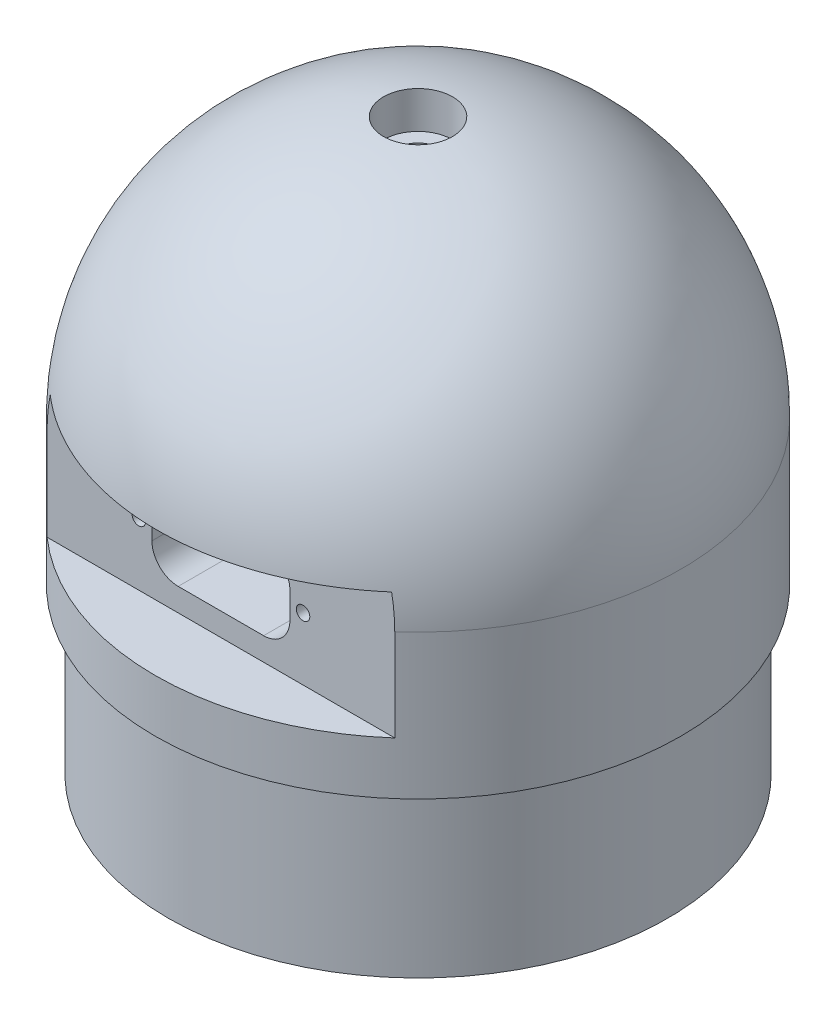
SolidWorks part; units mm, degrees
material "PE haute densité"
ref_plane "Plan de face" through (0, 0, 0) normal (0, 0, 1) x (1, 0, 0)
ref_plane "Plan de dessus" through (0, 0, 0) normal (0, 1, 0) x (1, 0, 0)
ref_plane "Plan de droite" through (0, 0, 0) normal (1, 0, 0) x (0, 0, -1)
sketch "Esquisse1" plane through (0, 0, 0) normal (0, 1, 0) x (1, 0, 0)
  circle A0 centre (0, 0) radius 40
extrude "Boss.-Extru.1" add sketch "Esquisse1" along normal blind 87
fillet "Congé1" radius 40 1 edges at (0, 87, 40)
sketch "Esquisse2" plane through (0, 0, 0) normal (0, -1, 0) x (1, 0, 0)
  circle A2 centre (0, 0) radius 38
  circle A3 centre (0, 0) radius 38
  dimension "D1" = 2
extrude "Enlèv. mat.-Extru.1" cut sketch "Esquisse2" against normal blind 25 flip side to cut
sketch "Esquisse3" plane through (0, 0, 0) normal (0, 0, 1) x (1, 0, 0)
  line L1 (-38, 52) -> (38, 52)
  line L2 (-38, 33) -> (38, 33)
  line L3 (-38, 33) -> (38, 33)
  line L4 (-38, 33) -> (-38, 52)
  line L5 (38, 52) -> (38, 33)
  dimension "D1" = 33
  dimension "D2" = 19
extrude "Enlèv. mat.-Extru.2" cut sketch "Esquisse3" against normal blind 10 from offset 40
sketch "Esquisse4" plane through (0, 0, 30) normal (0, 0, 1) x (1, 0, 0)
  line L0 (0, 52) -> (0, 33) construction
  line L1 (-25.9808, 52) -> (25.9808, 52) construction
  line L2 (26.4575, 33) -> (-26.4575, 33) construction
  line L6 (-6.5, 36.5) -> (6.5, 36.5)
  line L7 (-6.5, 48.5) -> (6.5, 48.5)
  line L8 (-10.5, 44.5) -> (-10.5, 40.5)
  line L9 (10.5, 44.5) -> (10.5, 40.5)
  line L10 (-10.5, 52) -> (-10.5, 33) construction
  line L12 (10.5, 52) -> (10.5, 33) construction
  line L30 (-12.5, 52) -> (-12.5, 33) construction
  line L31 (12.5, 52) -> (12.5, 33) construction
  arc A0 (-10.5, 40.5) -> (-6.5, 36.5) centre (-6.5, 40.5) ccw
  arc A1 (6.5, 36.5) -> (10.5, 40.5) centre (6.5, 40.5) ccw
  arc A2 (10.5, 44.5) -> (6.5, 48.5) centre (6.5, 44.5) ccw
  arc A3 (-6.5, 48.5) -> (-10.5, 44.5) centre (-6.5, 44.5) ccw
  dimension "D5" = 4
  dimension "D1" = 12
  dimension "D2" = 10.5
  dimension "D3" = 10.5
  dimension "D7" = 12.5
  dimension "D8" = 12.5
extrude "Enlèv. mat.-Extru.3" cut sketch "Esquisse4" against normal blind 20
sketch "Esquisse5" plane through (0, 0, 0) normal (0, -1, 0) x (1, 0, 0)
  line L0 (-45, 0) -> (45, 0) construction
  line L1 (0.3742, 42.8729) -> (0.3742, -43.7282) construction
  line L2 (-14, 18) -> (16, 18)
  line L3 (16, 18) -> (16, 22)
  line L4 (16, 22) -> (24, 22)
  line L5 (24, 22) -> (24, -22)
  line L6 (24, -22) -> (16, -22)
  line L7 (16, -22) -> (16, -18)
  line L8 (16, -18) -> (-14, -18)
  line L9 (-14, 18) -> (-14, 20.5)
  line L10 (-14, 20.5) -> (-17, 20.5)
  line L11 (-17, 20.5) -> (-17, 18)
  line L12 (-14, -18) -> (-14, -20.5)
  line L13 (-14, -20.5) -> (-17, -20.5)
  line L14 (-17, -20.5) -> (-17, -18)
  line L15 (-27, 8) -> (-27, -8)
  line L16 (-27, 8) -> (-17, 18)
  line L17 (-27, -8) -> (-17, -18)
  point P12 (-45.3854, -20.6)
  point P13 (46.1338, -20.6)
  point P19 (-28, 0)
  point P20 (-28, -22)
  point P21 (-45.3854, -12)
  point P22 (46.1338, -12)
extrude "Enlèv. mat.-Extru.4" cut sketch "Esquisse5" against normal blind 68
sketch "Esquisse6" plane through (0, 68, 0) normal (0, -1, 0) x (1, 0, 0)
  circle A0 centre (0, 0) radius 3.1
extrude "Enlèv. mat.-Extru.5" cut sketch "Esquisse6" against normal up to next
ref_plane "Plan1" through (0, 87, 0) normal (0, -1, 0) x (1, 0, 0)
sketch "Esquisse8" plane through (0, 87, 0) normal (0, -1, 0) x (1, 0, 0)
  circle A0 centre (0, 0) radius 5.25
extrude "Enlèv. mat.-Extru.6" cut sketch "Esquisse8" along normal blind 6
sketch "Esquisse11" plane through (0, 0, 0) normal (0, 0, 1) x (1, 0, 0)
  line L0 (-27, 47) -> (-27, 41)
  line L1 (-27, 47) -> (-45, 47)
  line L2 (-27, 41) -> (-45, 30.6077)
  line L3 (-45, 30.6077) -> (-45, 47)
  dimension "D1" = 30
revolve "Enlèvement de matière-Révolution1" cut sketch "Esquisse11" angle 360 about L1
hole_wizard "Trou taraudé M2.51" positions "Esquisse21" profile "Esquisse20" tap size "M2.5" standard "ISO" end condition up to next
sketch "Esquisse21" plane through (0, 0, 30) normal (0, 0, 1) x (1, 0, 0)
  point P0 (-12.5, 42.5)
  point P2 (12.5, 42.5)
sketch "Esquisse20" plane through (-12.5, 42.5, 30) normal (1, 0, 0) x (0, -1, 0)
  line L0 (0, 0) -> (0, 12)
  line L1 (0, 12) -> (1.025, 12)
  line L2 (1.025, 12) -> (1.025, 0)
  line L5 (1.025, 0) -> (0, 0)
  line L11 (0, -6.35) -> (0, 107.95) construction
  dimension "Diamètre du trou pour taraudage jusqu'au prochain" = 2.05
  dimension "Profondeur du trou pour taraudage jusqu'au prochain" = 12
cosmetic thread "Filetage de perçage1" parameters "D2"=2.5
cosmetic thread "Filetage de perçage2" parameters "D2"=2.5
hole_wizard "Trou taraudé M51" positions "Esquisse23" profile "Esquisse22" tap size "M5" standard "ISO"
sketch "Esquisse23" plane through (-17, 0, 0) normal (1, 0, 0) x (0, 0, -1)
  point P0 (14, 21)
sketch "Esquisse22" plane through (-17, 21, -14) normal (0, 1, 0) x (0, 0, -1)
  line L0 (0, 0) -> (0, 18.327)
  line L1 (0, 18.327) -> (2.1, 18.327)
  line L2 (2.1, 18.327) -> (2.1, 0)
  line L5 (2.1, 0) -> (0, 0)
  line L11 (0, -6.35) -> (0, 107.95) construction
  dimension "Diamètre du trou pour taraudage jusqu'au prochain" = 4.2
  dimension "Profondeur du trou pour taraudage jusqu'au prochain" = 18.327
cosmetic thread "Filetage de perçage3" parameters "D2"=5
